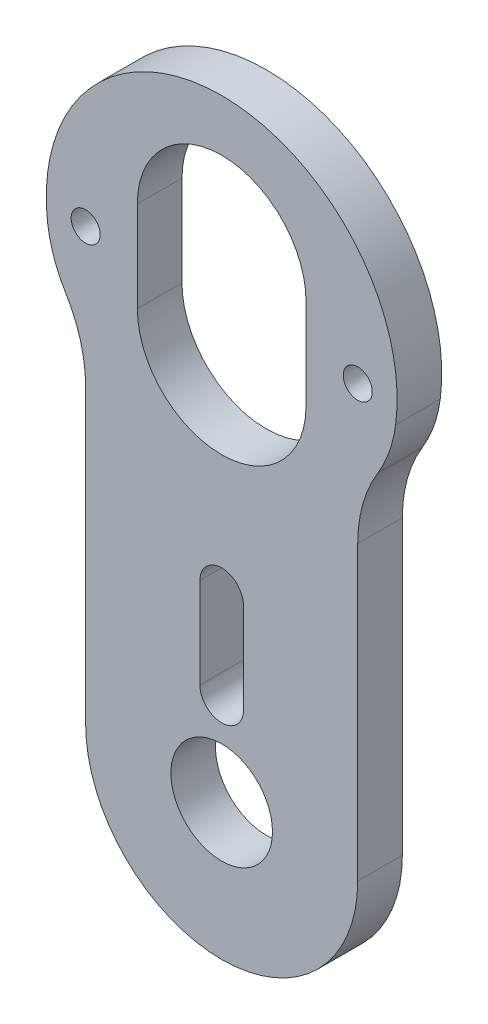
SolidWorks part; units mm, degrees
ref_plane "Alzado" through (0, 0, 0) normal (0, 0, 1) x (1, 0, 0)
ref_plane "Planta" through (0, 0, 0) normal (0, 1, 0) x (1, 0, 0)
ref_plane "Vista lateral" through (0, 0, 0) normal (1, 0, 0) x (0, 0, -1)
sketch "Croquis1" plane through (0, 0, 0) normal (0, 0, 1) x (1, 0, 0)
  line L0 (0, 0) -> (0, 33.3375) construction
  line L3 (-9.525, 0) -> (-9.525, 33.3375)
  line L6 (9.525, 0) -> (9.525, 33.3375)
  line L9 (0, 6.35) -> (0, 12.7) construction
  line L10 (-1.524, 6.35) -> (-1.524, 12.7)
  line L11 (1.524, 6.35) -> (1.524, 12.7)
  line L12 (0, 33.3375) -> (0, 26.9875) construction
  line L13 (5.9055, 33.3375) -> (5.9055, 26.9875)
  line L14 (-5.9055, 33.3375) -> (-5.9055, 26.9875)
  arc A8 (-9.525, 0) -> (9.525, 0) centre (0, 0) ccw
  arc A9 (9.525, 33.3375) -> (-9.525, 33.3375) centre (0, 33.3375) ccw
  circle A10 centre (0, 0) radius 3.556
  arc A11 (-1.524, 6.35) -> (1.524, 6.35) centre (0, 6.35) ccw
  arc A12 (1.524, 12.7) -> (-1.524, 12.7) centre (0, 12.7) ccw
  arc A13 (5.9055, 33.3375) -> (-5.9055, 33.3375) centre (0, 33.3375) ccw
  arc A14 (-5.9055, 26.9875) -> (5.9055, 26.9875) centre (0, 26.9875) ccw
  circle A15 centre (0, 30.1625) radius 5.9055
  point P2 (0, 16.6687)
  point P12 (0, 9.525)
  point P17 (0, 30.1625)
  dimension "D2" = 6.35
  dimension "D1" = 6.35
  dimension "D3" = 3.048
  dimension "D4" = 7.112
  dimension "D7" = 9.525
  dimension "D5" = 6.35
  dimension "D6" = 26.9875
  dimension "D8" = 11.811
  dimension "D9" = 3.6195
extrude "Saliente-Extruir1" add sketch "Croquis1" along normal blind 3.1242 contours L6 A9 L3 A8 A14 L14 A13 L13 A12 L11 A11 L10 A10
sketch "Croquis2" plane through (0, 0, 3.1242) normal (0, 0, 1) x (1, 0, 0)
  line L0 (0, 33.3375) -> (0, 26.9875) construction
  line L1 (-3.175, 30.1625) -> (3.175, 30.1625) construction
  line L2 (-3.175, 39.243) -> (3.175, 39.243)
  line L3 (-3.175, 21.082) -> (3.175, 21.082)
  line L4 (-9.525, 0) -> (-9.525, 33.3375) construction
  line L5 (9.525, 0) -> (9.525, 33.3375) construction
  circle A0 centre (0, 33.3375) radius 5.9055
  circle A1 centre (0, 26.9875) radius 5.9055
  arc A2 (5.9055, 33.3375) -> (-5.9055, 33.3375) centre (0, 33.3375) ccw construction
  arc A3 (-3.175, 39.243) -> (-3.175, 21.082) centre (-3.175, 30.1625) ccw
  arc A4 (3.175, 21.082) -> (3.175, 39.243) centre (3.175, 30.1625) ccw
  arc A5 (-12.1781, 28.9795) -> (0, 42.8625) centre (0, 30.5797) cw
  arc A6 (9.525, 33.3375) -> (-9.525, 33.3375) centre (0, 33.3375) ccw construction
  arc A7 (0, 42.8625) -> (12.1781, 28.9795) centre (0, 30.5797) cw
  arc A8 (-10.9229, 25.4269) -> (-9.525, 20.4595) centre (-19.05, 20.4595) cw
  arc A9 (10.9229, 25.4269) -> (9.525, 20.4595) centre (19.05, 20.4595) ccw
  circle A10 centre (-9.525, 30.1625) radius 1.016
  circle A11 centre (9.525, 30.1625) radius 1.016
  circle A12 centre (9.525, 30.1625) radius 1.016
  point P12 (0, 30.1625)
  arc M5 (5.9055, 26.9875) -> (-5.9055, 26.9875) centre (0, 26.9875) cw
  arc M7 (-5.9055, 33.3375) -> (5.9055, 33.3375) centre (0, 33.3375) cw
  line M8 (5.9055, 33.3375) -> (5.9055, 26.9875)
  line M14 (9.525, 0) -> (9.525, 33.3375)
  arc M15 (9.525, 33.3375) -> (-9.525, 33.3375) centre (0, 33.3375) ccw
  line M16 (-9.525, 33.3375) -> (-9.525, 0)
  dimension "D1" = 9.525
  dimension "D2" = 2.032
  dimension "D3" = 6.35
extrude "Saliente-Extruir3" add sketch "Croquis2" against normal blind 3.1242 contours A7 A4 M15 | A4 A3 L2 M15 | A5 A3 M15 | A3 A10 M15 M16 | A4 A11 M14 M15 | A9 A4 M14 | A3 A8 M16 | A4 L2 L3 M15 M7 M8 M5 M14
sketch "Croquis3" plane through (0, 0, 3.1242) normal (0, 0, 1) x (1, 0, 0)
  circle A0 centre (-9.525, 30.1625) radius 1.016
  circle A1 centre (9.525, 30.1625) radius 1.016
  circle A2 centre (-9.525, 30.1625) radius 1.016 construction
  circle A3 centre (9.525, 30.1625) radius 1.016 construction
extrude "Cortar-Extruir1" cut sketch "Croquis3" against normal through all
